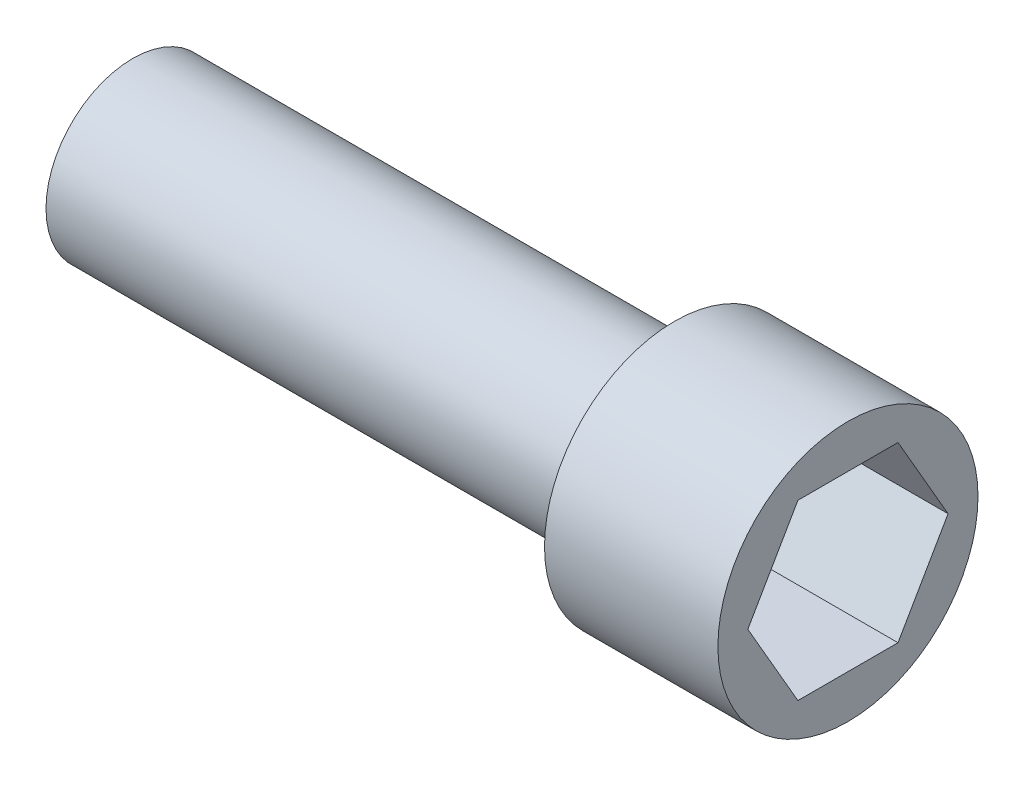
SolidWorks part; units mm, degrees
ref_plane "Front Plane" through (0, 0, 0) normal (0, 0, 1) x (1, 0, 0)
ref_plane "Top Plane" through (0, 0, 0) normal (0, 1, 0) x (1, 0, 0)
ref_plane "Right Plane" through (0, 0, 0) normal (1, 0, 0) x (0, 0, -1)
sketch "Sketch1" plane through (0, 0, 0) normal (0, 0, 1) x (1, 0, 0)
  line L0 (16.5, 0) -> (-16.5, 0)
  line L1 (-16.5, 0) -> (-16.5, 4)
  line L2 (-16.5, 4) -> (8.5, 4)
  line L3 (8.5, 4) -> (8.5, 6)
  line L4 (8.5, 6) -> (16.5, 6)
  line L5 (16.5, 6) -> (16.5, 0)
  dimension "D1" = 25
  dimension "D2" = 8
  dimension "D3" = 4
  dimension "D4" = 2
  dimension "D5" = 16.5
revolve "Revolve1" add sketch "Sketch1" angle 360 about L0
sketch "Sketch2" plane through (16.5, 0, 0) normal (1, 0, 0) x (0, 0, -1)
  line L1 (4.6188, 0) -> (2.3094, 4)
  line L2 (2.3094, 4) -> (-2.3094, 4)
  line L3 (-2.3094, 4) -> (-4.6188, 0)
  line L4 (-4.6188, 0) -> (-2.3094, -4)
  line L5 (-2.3094, -4) -> (2.3094, -4)
  line L6 (2.3094, -4) -> (4.6188, 0)
  circle A0 centre (0, 0) radius 4 construction
  point P1 (0, 0)
  dimension "D1" = 8
extrude "Cut-Extrude1" cut sketch "Sketch2" against normal blind 6
